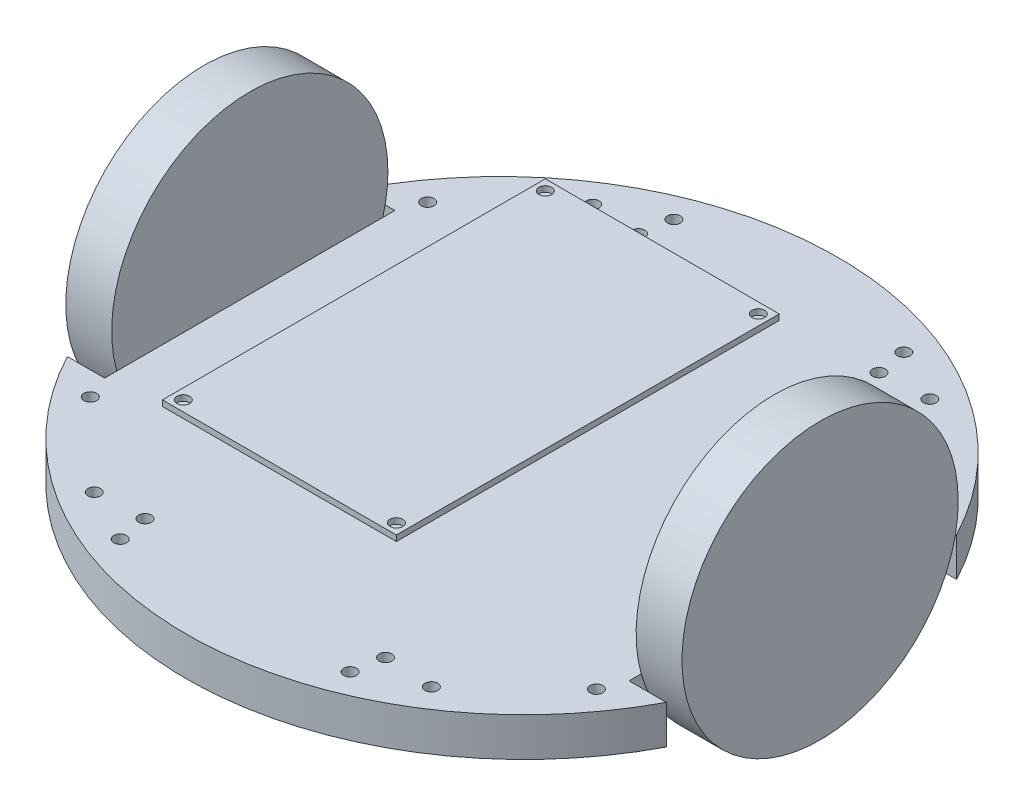
SolidWorks part; units mm, degrees
ref_plane "Front Plane" through (0, 0, 0) normal (0, 0, 1) x (1, 0, 0)
ref_plane "Top Plane" through (0, 0, 0) normal (0, 1, 0) x (1, 0, 0)
ref_plane "Right Plane" through (0, 0, 0) normal (1, 0, 0) x (0, 0, -1)
sketch "Sketch2" plane through (0, 0, 0) normal (0, 1, 0) x (1, 0, 0)
  line L0 (74.6125, 72.3392) -> (74.6125, 117.4242)
  line L1 (0, 72.3392) -> (149.225, 72.3392)
  line L2 (0, 72.3392) -> (0, 0)
  line L3 (0, 0) -> (149.225, 0)
  line L4 (149.225, 72.3392) -> (149.225, 0)
  line L6 (0, 72.3392) -> (9.271, 72.3392)
  line L7 (0, 72.3392) -> (0, 0)
  line L8 (0, 0) -> (9.271, 0)
  line L9 (9.271, 72.3392) -> (9.271, 0)
  line L10 (149.225, 72.3392) -> (139.954, 72.3392)
  line L11 (149.225, 72.3392) -> (149.225, 0)
  line L12 (149.225, 0) -> (139.954, 0)
  line L13 (139.954, 72.3392) -> (139.954, 0)
  arc A1 (0, 72.3392) -> (149.225, 72.3392) centre (74.6125, 33.1425) cw
  dimension "D1" = 149.225
  dimension "D3" = 0
  dimension "D5" = 9.271
  dimension "D2" = 72.3392
  dimension "D4" = 45.085
  dimension "D6" = 9.271
extrude "Boss-Extrude1" add sketch "Sketch2" along normal blind 9.652 contours A1 L1 L0 | A1 L0 L1 | L13 L1 L9 L3
sketch "Sketch4" plane through (0, 0, 0) normal (0, -1, 0) x (1, 0, 0)
  line L0 (139.954, -72.3392) -> (149.225, -72.3392) construction
  line L2 (139.954, -72.3392) -> (139.954, 0) construction
  line L3 (0, -72.3392) -> (9.271, -72.3392) construction
  circle A2 centre (116.6197, -98.2703) radius 1.5875
  arc A3 (7.7555, -72.3392) -> (141.4695, -72.3392) centre (74.6125, -33.1425) ccw
  arc A4 (0, -72.3392) -> (149.225, -72.3392) centre (74.6125, -33.1425) ccw construction
  circle A5 centre (137.668, -78.2007) radius 1.5875
  circle A6 centre (103.2523, -105.1564) radius 1.5875
  circle A7 centre (104.5706, -97.6513) radius 1.5875
  dimension "D1" = 3.175
  dimension "D3" = 29.083
  dimension "D4" = 0
  dimension "D5" = 0
  dimension "D6" = 6.7818
  dimension "D7" = 3.175
  dimension "D2" = 2.286
  dimension "D8" = 3.175
  dimension "D9" = 15.0368
  dimension "D10" = 3.175
  dimension "D11" = 12.065
  dimension "D12" = 7.62
extrude "Cut-Extrude1" cut sketch "Sketch4" against normal blind 9.652 contours A7 | A6 | A2 | A5
sketch "Sketch5" plane through (0, 0, 0) normal (0, -1, 0) x (1, 0, 0)
  line L0 (74.6125, 0) -> (74.6125, -117.4242)
  line L1 (9.271, 0) -> (139.954, 0) construction
  line L2 (9.271, -36.1696) -> (139.954, -36.1696)
  line L3 (9.271, -72.3392) -> (9.271, 0) construction
  line L4 (139.954, -72.3392) -> (139.954, 0) construction
  arc A0 (0, -72.3392) -> (149.225, -72.3392) centre (74.6125, -33.1425) ccw construction
  dimension "D1" = 0
ref_plane "Plane1" through (74.6125, 0, 0) normal (1, 0, 0) x (0, 0, -1)
ref_plane "Plane2" through (0, 0, -36.1696) normal (0, 0, 1) x (1, 0, 0)
mirror "Mirror1" about plane through (0, 0, -36.1696) normal (0, 0, 1) of "Boss-Extrude1"
mirror "Mirror2" about plane through (74.6125, 0, 0) normal (1, 0, 0) of "Cut-Extrude1"
mirror "Mirror3" about plane through (0, 0, -36.1696) normal (0, 0, 1) of "Mirror2", "Cut-Extrude1"
sketch "Sketch6" plane through (139.954, 0, 0) normal (1, 0, 0) x (0, 0, -1)
  line L0 (36.1696, 71.8756) -> (36.1696, -71.8756) construction
  line L2 (72.3392, 0) -> (0, 0) construction
  circle A0 centre (36.1696, 18.923) radius 34.417
  dimension "D1" = 68.834
  dimension "D2" = 0
  dimension "D3" = 18.923
extrude "Boss-Extrude2" add sketch "Sketch6" along normal blind 11.43
ref_plane "Plane3" through (0, 32.512, 0) normal (0, 1, 0) x (1, 0, 0)
sketch "Sketch7" plane through (0, 32.512, 0) normal (0, 1, 0) x (1, 0, 0)
  line L0 (74.6125, -5.3086) -> (74.6125, 5.3086) construction
  line L1 (45.466, 73.6092) -> (103.759, 73.6092)
  line L2 (45.466, 73.6092) -> (45.466, -21.7932)
  line L3 (45.466, -21.7932) -> (103.759, -21.7932)
  line L4 (103.759, 73.6092) -> (103.759, -21.7932)
  line L5 (-71.8756, 36.1696) -> (71.8756, 36.1696) construction
  dimension "D1" = 58.293
  dimension "D2" = 95.4024
  dimension "D3" = 29.1465
  dimension "D4" = 37.4396
extrude "Boss-Extrude3" add sketch "Sketch7" along normal blind 1.4224 separate body
sketch "Sketch8" plane through (0, 33.9344, 0) normal (0, 1, 0) x (1, 0, 0)
  line L0 (45.466, -21.7932) -> (103.759, -21.7932) construction
  line L1 (103.759, -21.7932) -> (103.759, 73.6092) construction
  line L2 (45.466, 73.6092) -> (45.466, -21.7932) construction
  line L3 (103.759, 73.6092) -> (45.466, 73.6092) construction
  circle A0 centre (101.1555, -19.1897) radius 1.5875
  circle A1 centre (48.0695, -19.1897) radius 1.5875
  circle A2 centre (101.1555, 71.0057) radius 1.5875
  circle A3 centre (48.0695, 71.0057) radius 1.5875
  dimension "D1" = 3.175
  dimension "D2" = 3.175
  dimension "D3" = 2.6035
  dimension "D4" = 2.6035
  dimension "D5" = 2.6035
  dimension "D6" = 2.6035
  dimension "D7" = 3.175
  dimension "D8" = 3.175
  dimension "D9" = 2.6035
  dimension "D10" = 2.6035
  dimension "D11" = 2.6035
  dimension "D12" = 2.6035
extrude "Cut-Extrude2" cut sketch "Sketch8" against normal blind 1.4224
mirror "Mirror4" about plane through (74.6125, 0, 0) normal (1, 0, 0) of "Boss-Extrude2"
